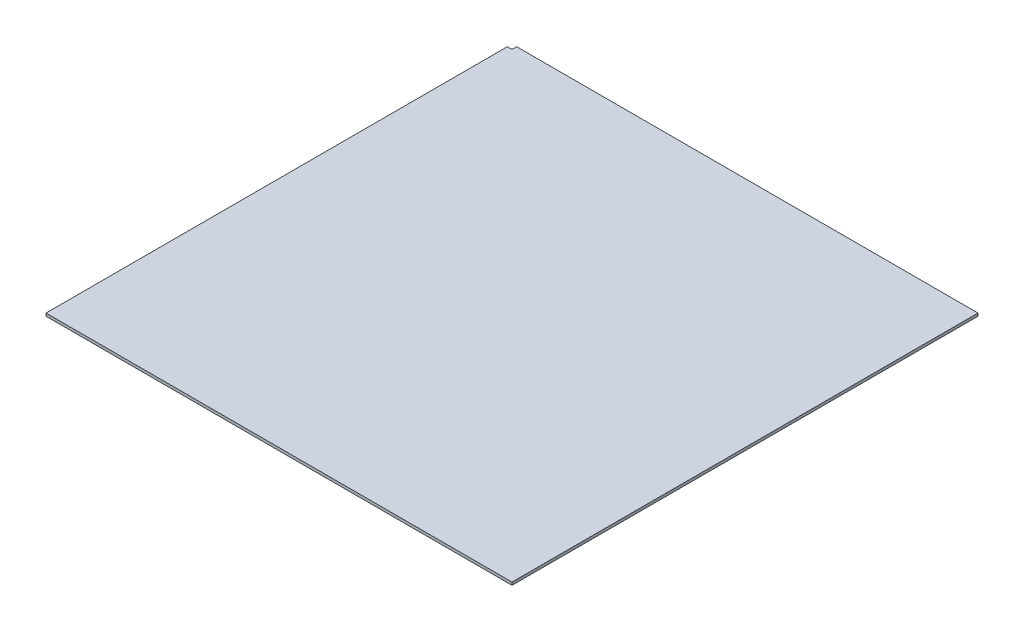
SolidWorks part; units mm, degrees
material "Acrílico (médio-alto impacto)"
ref_plane "Plano frontal" through (0, 0, 0) normal (0, 0, 1) x (1, 0, 0)
ref_plane "Plano superior" through (0, 0, 0) normal (0, 1, 0) x (1, 0, 0)
ref_plane "Plano direito" through (0, 0, 0) normal (1, 0, 0) x (0, 0, -1)
sketch "Esboço1" plane through (0, 0, 0) normal (0, 1, 0) x (1, 0, 0)
  line L1 (-490, 500) -> (500, 500)
  line L2 (-500, 490) -> (-500, -500)
  line L3 (-500, -500) -> (500, -500)
  line L4 (500, 500) -> (500, -500)
  line L5 (-500, 500) -> (500, -500) construction
  line L6 (-500, -500) -> (500, 500) construction
  line L9 (-500, 490) -> (-490, 490)
  line L10 (-490, 500) -> (-490, 490)
  point P0 (0, 0)
  dimension "D1" = 1000
  dimension "D2" = 1000
  dimension "D3" = 10
extrude "Ressalto-extrusão1" add sketch "Esboço1" along normal mid plane 6
